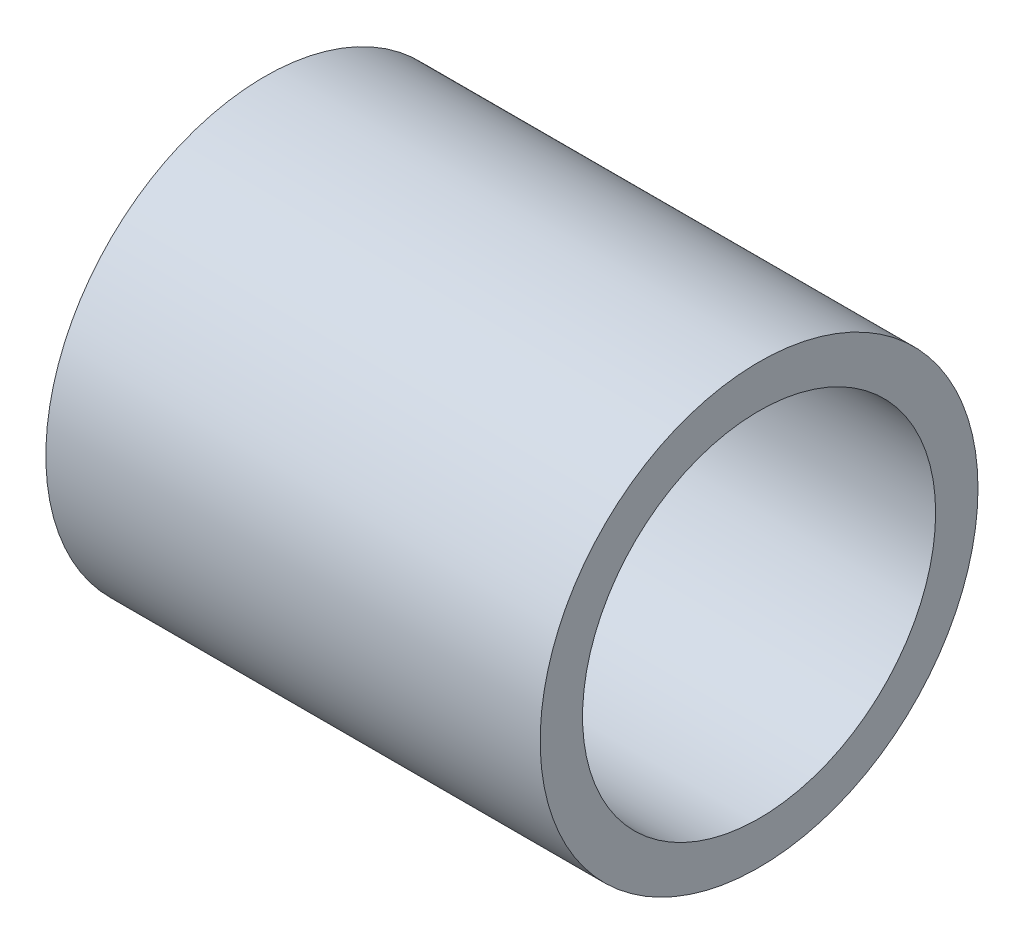
SolidWorks part; units mm, degrees
material "Stal stopowa"
ref_plane "Płaszczyzna przednia" through (0, 0, 0) normal (0, 0, 1) x (1, 0, 0)
ref_plane "Płaszczyzna górna" through (0, 0, 0) normal (0, 1, 0) x (1, 0, 0)
ref_plane "Płaszczyzna prawa" through (0, 0, 0) normal (1, 0, 0) x (0, 0, -1)
sketch "Szkic1" plane through (0, 0, 0) normal (1, 0, 0) x (0, 0, -1)
  circle A0 centre (0, 0) radius 12.5
  circle A1 centre (0, 0) radius 15.5
  dimension "D1" = 25
  dimension "D2" = 31
extrude "Dodanie-wyciągnięcie1" add sketch "Szkic1" along normal blind 35
